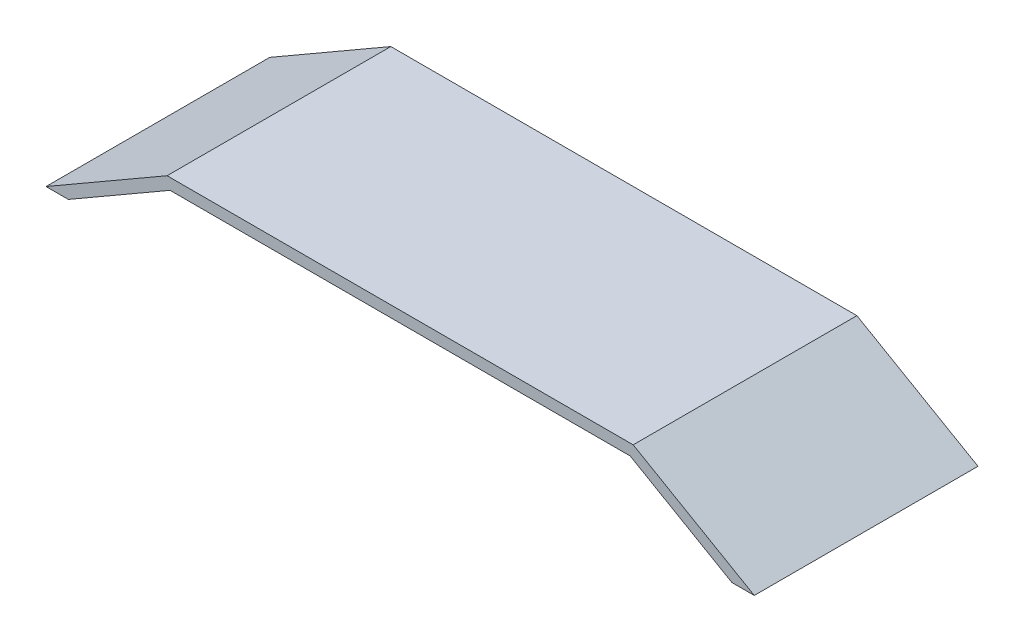
SolidWorks part; units mm, degrees
ref_plane "前视基准面" through (0, 0, 0) normal (0, 0, 1) x (1, 0, 0)
ref_plane "上视基准面" through (0, 0, 0) normal (0, 1, 0) x (1, 0, 0)
ref_plane "右视基准面" through (0, 0, 0) normal (1, 0, 0) x (0, 0, -1)
sketch "草图1" plane through (0, 0, 0) normal (0, 0, 1) x (1, 0, 0)
  line L0 (-250, 0) -> (250, 0)
  line L1 (-250, 0) -> (-379.9038, -75)
  line L2 (250, 0) -> (379.9038, -75)
  line L3 (-246.7846, -12) -> (-355.9038, -75)
  line L4 (-246.7846, -12) -> (246.7846, -12)
  line L5 (246.7846, -12) -> (355.9038, -75)
  line L6 (-379.9038, -75) -> (-355.9038, -75)
  line L7 (-250, 0) -> (-536.9445, -165.6675) construction
  line L8 (250, 0) -> (766.6014, -298.26) construction
  line L9 (246.7846, -12) -> (760.6014, -308.6523) construction
  line L10 (355.9038, -75) -> (379.9038, -75)
  line L11 (-246.7846, -12) -> (-530.9445, -176.0598) construction
  dimension "D1" = 150
  dimension "D2" = 150
  dimension "D4" = 75
  dimension "D3" = 12
extrude "凸台-拉伸1" add sketch "草图1" along normal blind 240
